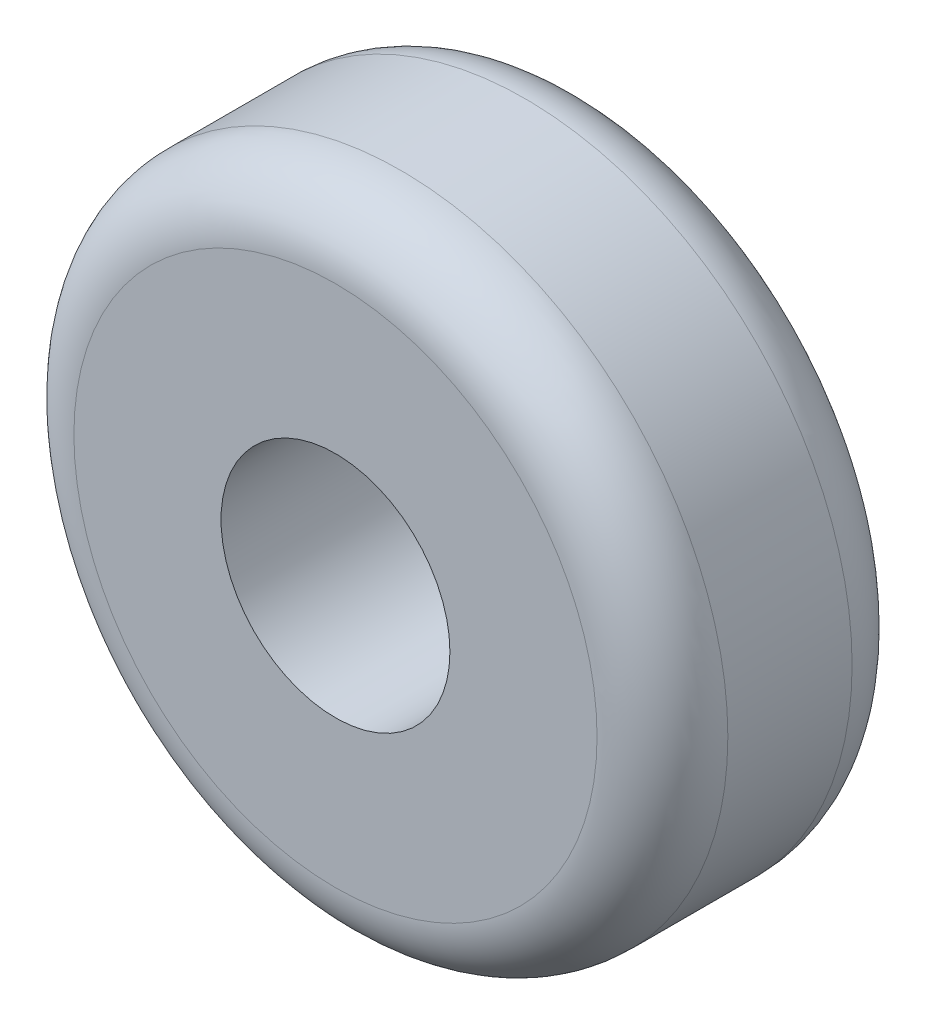
SolidWorks part; units mm, degrees
ref_plane "Plan de face" through (0, 0, 0) normal (0, 0, 1) x (1, 0, 0)
ref_plane "Plan de dessus" through (0, 0, 0) normal (0, 1, 0) x (1, 0, 0)
ref_plane "Plan de droite" through (0, 0, 0) normal (1, 0, 0) x (0, 0, -1)
sketch "Esquisse1" plane through (0, 0, 0) normal (0, 0, 1) x (1, 0, 0)
  circle A0 centre (0, 0) radius 17.5
  circle A1 centre (0, 0) radius 0.8947
  circle A2 centre (0, 0) radius 50
  dimension "D1" = 35
  dimension "D2" = 100
extrude "Boss.-Extru.1" add sketch "Esquisse1" along normal blind 39 contours A2 A0
fillet "Congé1" radius 10 2 edges at (50, 0, 0) (50, 0, 39)
